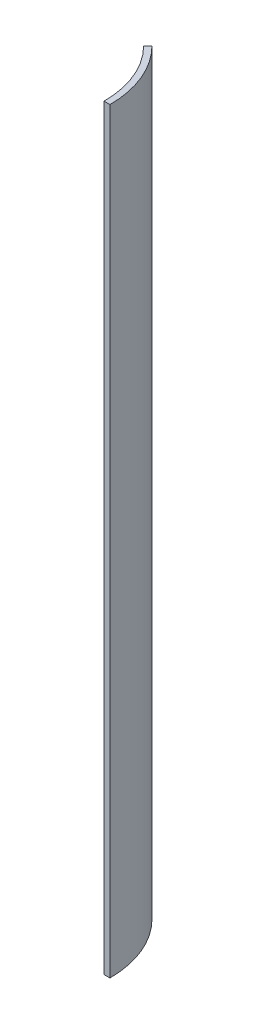
SolidWorks part; units mm, degrees
material "6061-T6 (SS)"
ref_plane "Front Plane" through (0, 0, 0) normal (0, 0, 1) x (1, 0, 0)
ref_plane "Top Plane" through (0, 0, 0) normal (0, 1, 0) x (1, 0, 0)
ref_plane "Right Plane" through (0, 0, 0) normal (1, 0, 0) x (0, 0, -1)
ref_axis "Axis1" through (0, 819.187, 0) along (0, -1, 0)
sketch "Sketch2" plane through (0, 0, 0) normal (0, 0, 1) x (1, 0, 0)
  line L0 (-69.85, 0) -> (-69.85, 520.7)
  line L1 (-65.786, 0) -> (-69.85, 0)
  line L2 (-65.786, 0) -> (-65.786, 520.7)
  line L3 (55, 0) -> (-55, 0) construction
  line L4 (-69.85, 260.35) -> (-65.786, 260.35) construction
  line L5 (0, 819.187) -> (0, -55) construction
  line L6 (-65.786, 520.7) -> (-69.85, 520.7)
  point P0 (-65.786, 0)
  point P1 (-69.85, 260.35)
  point P17 (-65.786, 260.35)
  dimension "D2" = 4.064
  dimension "D3" = 260.35
  dimension "D4" = 69.85
revolve "Revolve1" add sketch "Sketch2" angle 360 about axis through (0, 819.187, 0) along (0, -1, 0)
sketch "Sketch3" plane through (0, 0, 0) normal (0, 0, 1) x (1, 0, 0)
  line L1 (0, 819.187) -> (0, -55) construction
  line L2 (0, 562.8188) -> (133.2849, 562.8188)
  line L3 (0, 562.8188) -> (0, -51.9543)
  line L4 (0, -51.9543) -> (133.2849, -51.9543)
  line L5 (133.2849, 562.8188) -> (133.2849, -51.9543)
revolve "Cut-Revolve1" cut sketch "Sketch3" angle 315 about axis through (0, 819.187, 0) along (0, -1, 0)
